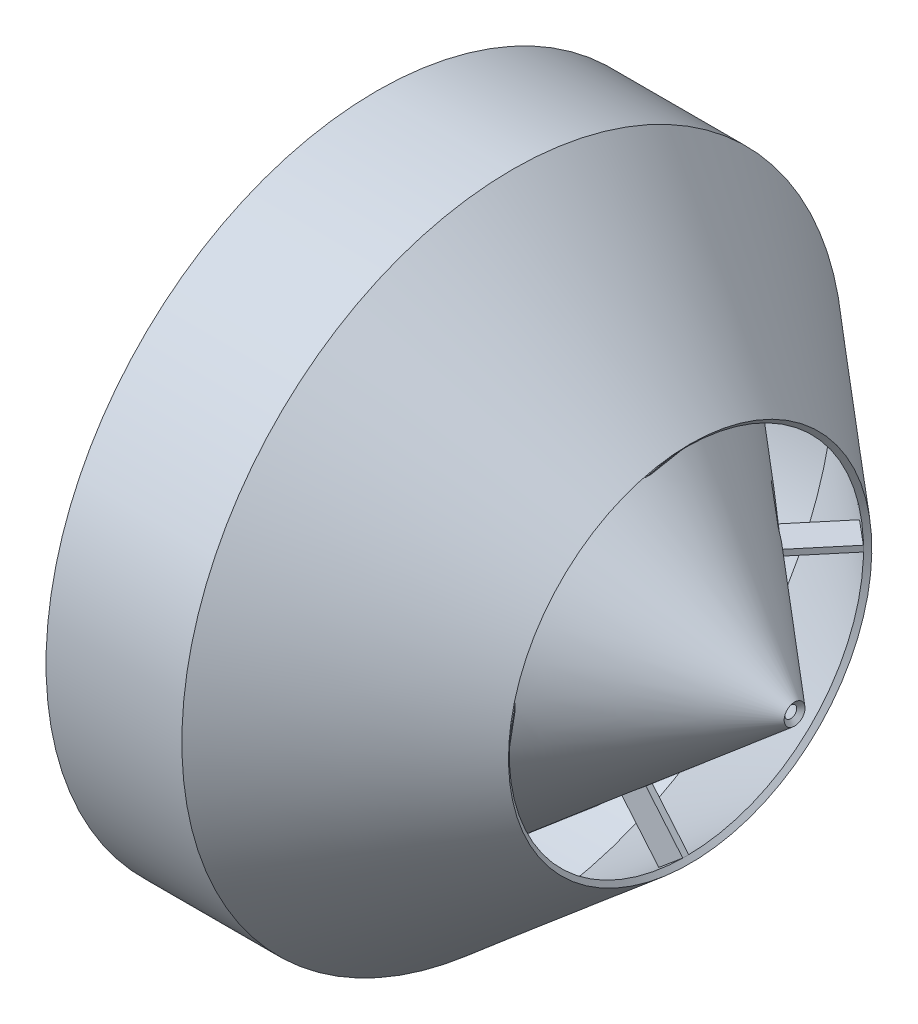
SolidWorks part; units mm, degrees
ref_plane "Front Plane" through (0, 0, 0) normal (0, 0, 1) x (1, 0, 0)
ref_plane "Top Plane" through (0, 0, 0) normal (0, 1, 0) x (1, 0, 0)
ref_plane "Right Plane" through (0, 0, 0) normal (1, 0, 0) x (0, 0, -1)
sketch "Sketch1" plane through (0, 0, 0) normal (0, 0, 1) x (1, 0, 0)
  line L0 (-30.4012, 69.85) -> (-1.6507, 69.85)
  line L1 (-1.6507, 69.85) -> (36.1875, 38.1)
  line L2 (36.1875, 38.1) -> (37.0038, 39.0729)
  line L3 (37.0038, 39.0729) -> (-1.1885, 71.12)
  line L4 (-1.1885, 71.12) -> (-30.4012, 71.12)
  line L5 (-30.4012, 71.12) -> (-30.4012, 69.85)
  line L6 (0, 0) -> (-327.6728, 0) construction
  point P2 (0, 67.9988)
  point P7 (0.368, 67.9389)
  point P10 (0, 0)
  point P12 (-29.5096, 68.58)
  point P13 (0.4029, 69.85)
  point P14 (1.4473, 68.58)
  point P15 (-30.4012, 68.58)
  point P16 (-1.6507, 70.3729)
  dimension "D1" = 1.27
  dimension "D2" = 1.27
  dimension "D3" = 69.85
  dimension "D4" = 38.1
  dimension "D5" = 40
revolve "Revolve1" add sketch "Sketch1" angle 360 about L6
sketch "Sketch2" plane through (0, 0, 0) normal (0, 0, 1) x (1, 0, 0)
  line L0 (0.7844, 49.8271) -> (1.6007, 50.8)
  line L2 (1.6007, 50.8) -> (59.4689, 2.2429)
  line L3 (59.4689, 2.2429) -> (58.6525, 1.27)
  line L4 (58.6525, 1.27) -> (0.7844, 49.8271)
  line L5 (0, 0) -> (-133.4917, 0) construction
  line L6 (-150.7017, 0) -> (-116.2816, 0) construction
  point P2 (1.6007, 50.8)
  dimension "D1" = 1.27
  dimension "D2" = 50.8
  dimension "D3" = 40
  dimension "D4" = 1.27
revolve "Revolve2" add sketch "Sketch2" angle 360 about L5
sketch "Sketch3" plane through (0, 0, 0) normal (0, 0, 1) x (1, 0, 0)
  line L0 (30.9521, 42.599) -> (36.1078, 38.2729)
  line L1 (36.1078, 38.2729) -> (27.4278, 27.9285)
  line L2 (27.4278, 27.9285) -> (22.2721, 32.2546)
  line L3 (22.2721, 32.2546) -> (30.9521, 42.599)
  line L4 (54.364, 0) -> (0, 0) construction
  point P7 (30.026, 43.3762)
  point P8 (27.4212, 27.9205)
  point P9 (22.2721, 32.2546)
  dimension "D1" = 40
extrude "Boss-Extrude1" add sketch "Sketch3" along normal mid plane 1.27
pattern_circular "CirPattern1" count 4 over 360 about axis through (0, 0, 0) along (1, 0, 0) of "Boss-Extrude1"
